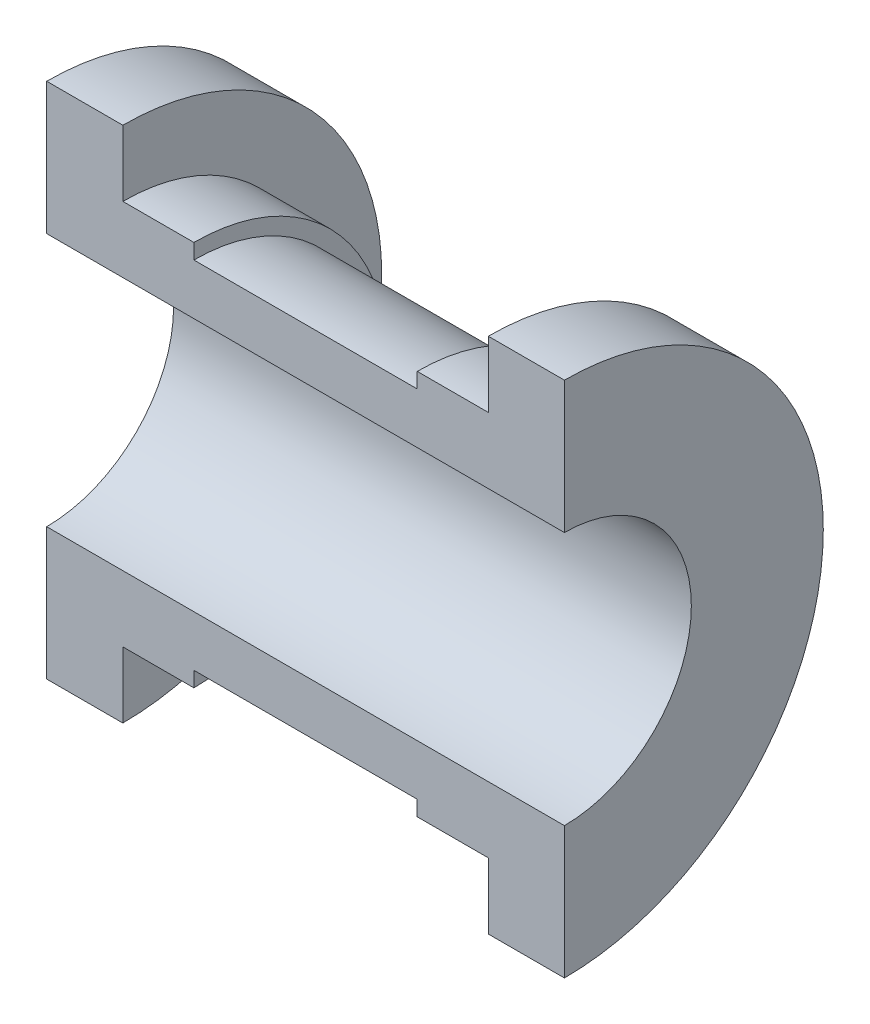
SolidWorks part; units mm, degrees
ref_plane "Front Plane" through (0, 0, 0) normal (0, 0, 1) x (1, 0, 0)
ref_plane "Top Plane" through (0, 0, 0) normal (0, 1, 0) x (1, 0, 0)
ref_plane "Right Plane" through (0, 0, 0) normal (1, 0, 0) x (0, 0, -1)
sketch "Sketch1" plane through (0, 0, 0) normal (0, 0, 1) x (1, 0, 0)
  line L0 (-27.0466, 0) -> (36.9933, 0) construction
  line L1 (25.5, 0) -> (25.5, 25.5)
  line L2 (25.5, 25.5) -> (18, 25.5)
  line L3 (18, 25.5) -> (18, 19)
  line L4 (18, 19) -> (11, 19)
  line L5 (11, 19) -> (11, 17.5)
  line L6 (11, 17.5) -> (3, 17.5)
  line L7 (-3, 17.5) -> (3, 17.5)
  line L9 (0, 0) -> (0, 68.3393) construction
  line L10 (-11, 19) -> (-11, 17.5)
  line L11 (-25.5, 0) -> (-25.5, 25.5)
  line L12 (-25.5, 25.5) -> (-18, 25.5)
  line L13 (-18, 25.5) -> (-18, 19)
  line L14 (-18, 19) -> (-11, 19)
  line L15 (-11, 17.5) -> (-3, 17.5)
  line L17 (25.5, 0) -> (-25.5, 0)
  point P22 (0, 23.5)
  dimension "D1" = 25.5
  dimension "D3" = 25.5
  dimension "D6" = 18
  dimension "D7" = 11
revolve "Revolve2" add sketch "Sketch1" angle 180 about L17
sketch "Sketch2" plane through (25.5, 0, 0) normal (1, 0, 0) x (0, 0, -1)
  line L0 (0, 25.5) -> (0, -25.5) construction
  line L1 (0, 12.5) -> (0, -12.5)
  arc A0 (0, -12.5) -> (0, 12.5) centre (0, 0) ccw
  dimension "D1" = 25
extrude "Cut-Extrude1" cut sketch "Sketch2" against normal through all
ref_plane "Plane2" through (0, 0, -17.5) normal (0, 0, 1) x (1, 0, 0)
sketch "Sketch3" plane through (0, 0, -17.5) normal (0, 0, 1) x (1, 0, 0)
  circle A0 centre (0, 0) radius 3
  dimension "D1" = 6
extrude "Boss-Extrude1" add sketch "Sketch3" against normal blind 6 separate body
